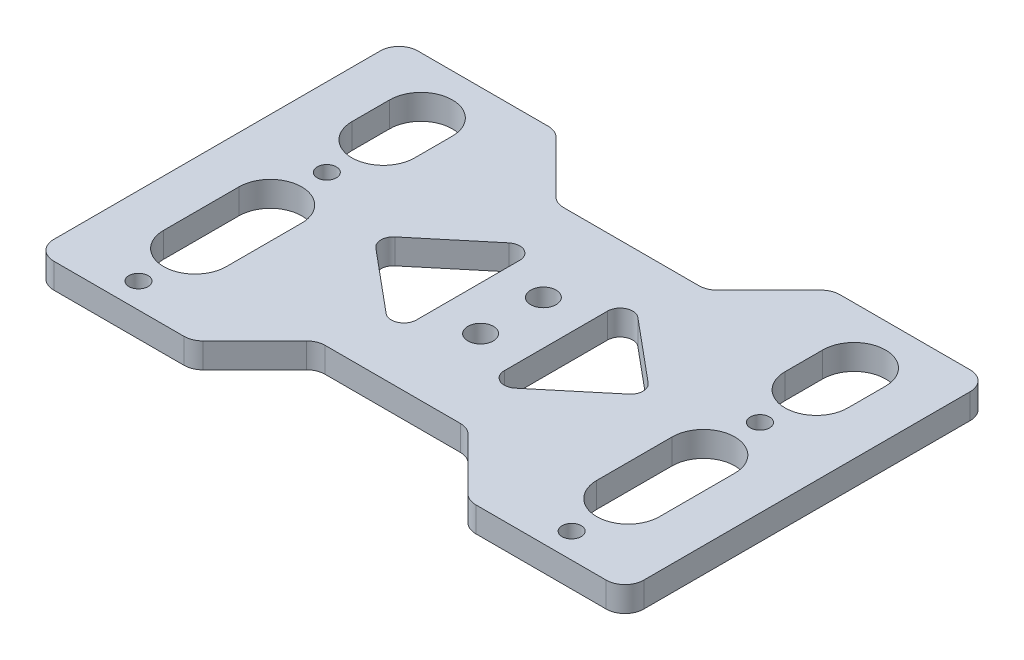
SolidWorks part; units mm, degrees
material "Thornel Mat VMA"
ref_plane "前视基准面" through (0, 0, 0) normal (0, 0, 1) x (1, 0, 0)
ref_plane "上视基准面" through (0, 0, 0) normal (0, 1, 0) x (1, 0, 0)
ref_plane "右视基准面" through (0, 0, 0) normal (1, 0, 0) x (0, 0, -1)
other "Configuration Table"
sketch "草图1" plane through (0, 0, 0) normal (0, 1, 0) x (1, 0, 0)
  line L1 (-47, -29) -> (47, -29)
  line L2 (-47, -29) -> (-47, 29)
  line L3 (-47, 29) -> (47, 29)
  line L4 (47, -29) -> (47, 29)
  line L5 (-47, -29) -> (47, 29) construction
  line L6 (-47, 29) -> (47, -29) construction
  point P0 (0, 0)
  dimension "D1" = 94
  dimension "D2" = 58
extrude "凸台-拉伸1" add sketch "草图1" along normal blind 4
fillet "圆角1" radius 3 4 edges at (47, 2, 29) (-47, 2, 29) (47, 2, -29) (-47, 2, -29)
sketch "草图2" plane through (0, 4, 0) normal (0, 1, 0) x (1, 0, 0)
  line L0 (-39.5, 14) -> (-39.5, 20) construction
  line L1 (-29.5, 20) -> (-29.5, 14) construction
  line L2 (-39.5, -16) -> (-39.5, -4) construction
  line L3 (-29.5, -4) -> (-29.5, -16) construction
  line L4 (-39.5, 14) -> (-39.5, 20)
  line L5 (-29.5, 20) -> (-29.5, 14)
  line L6 (-39.5, -16) -> (-39.5, -4)
  line L7 (-29.5, -4) -> (-29.5, -16)
  arc A0 (-29.5, 20) -> (-39.5, 20) centre (-34.5, 20) ccw construction
  arc A1 (-39.5, 14) -> (-29.5, 14) centre (-34.5, 14) ccw construction
  circle A2 centre (-34.5, 5) radius 1.525 construction
  arc A3 (-29.5, -4) -> (-39.5, -4) centre (-34.5, -4) ccw construction
  arc A4 (-39.5, -16) -> (-29.5, -16) centre (-34.5, -16) ccw construction
  circle A5 centre (-34.5, -25) radius 1.525 construction
  arc A6 (-29.5, 20) -> (-39.5, 20) centre (-34.5, 20) ccw
  arc A7 (-39.5, 14) -> (-29.5, 14) centre (-34.5, 14) ccw
  circle A8 centre (-34.5, 5) radius 1.525
  arc A9 (-29.5, -4) -> (-39.5, -4) centre (-34.5, -4) ccw
  arc A10 (-39.5, -16) -> (-29.5, -16) centre (-34.5, -16) ccw
  circle A11 centre (-34.5, -25) radius 1.525
extrude "切除-拉伸1" cut sketch "草图2" against normal blind 10
mirror "镜向1" about plane through (0, 0, 0) normal (1, 0, 0) of "切除-拉伸1"
sketch "草图3" plane through (0, 0, 0) normal (0, -1, 0) x (1, 0, 0)
  line L0 (-22, 29) -> (-12, 19)
  line L1 (-44, 29) -> (44, 29) construction
  line L2 (-12, 19) -> (12, 19)
  line L3 (12, 19) -> (22, 29)
  line L4 (22, 29) -> (-22, 29)
  point P5 (0, 19)
  dimension "D1" = 44
  dimension "D2" = 10
  dimension "D3" = 45
extrude "切除-拉伸2" cut sketch "草图3" against normal blind 10
mirror "镜向2" about plane through (0, 0, 0) normal (0, 0, 1) of "切除-拉伸2"
sketch "草图4" plane through (0, 0, 0) normal (0, -1, 0) x (1, 0, 0)
  line L0 (0, -5) -> (0, 5) construction
  circle A0 centre (0, 5) radius 2.025
  circle A1 centre (0, -5) radius 2.025
  dimension "D1" = 4.05
  dimension "D2" = 10
extrude "切除-拉伸3" cut sketch "草图4" against normal blind 10
sketch "草图5" plane through (0, 0, 0) normal (0, -1, 0) x (1, 0, 0)
  line L0 (-7, 12.5) -> (-7, -12.5)
  line L1 (-7, -12.5) -> (-22, 0)
  line L2 (-22, 0) -> (-7, 12.5)
  line L4 (0, 0) -> (0, -19) construction
  line L5 (-12, -19) -> (12, -19) construction
  line L6 (22, 0) -> (7, 12.5)
  line L7 (7, -12.5) -> (22, 0)
  line L8 (7, 12.5) -> (7, -12.5)
  dimension "D1" = 7
  dimension "D2" = 25
extrude "切除-拉伸4" cut sketch "草图5" against normal blind 10
fillet "圆角2" radius 2 6 edges at (7, 2, 12.5) (22, 2, 0) (7, 2, -12.5) (-7, 2, -12.5) (-22, 2, 0) (-7, 2, 12.5)
fillet "圆角3" radius 3 8 edges at (-12, 2, -19) (12, 2, -19) (22, 2, -29) (22, 2, 29) (12, 2, 19) (-22, 2, 29) (-22, 2, -29) (-12, 2, 19)
